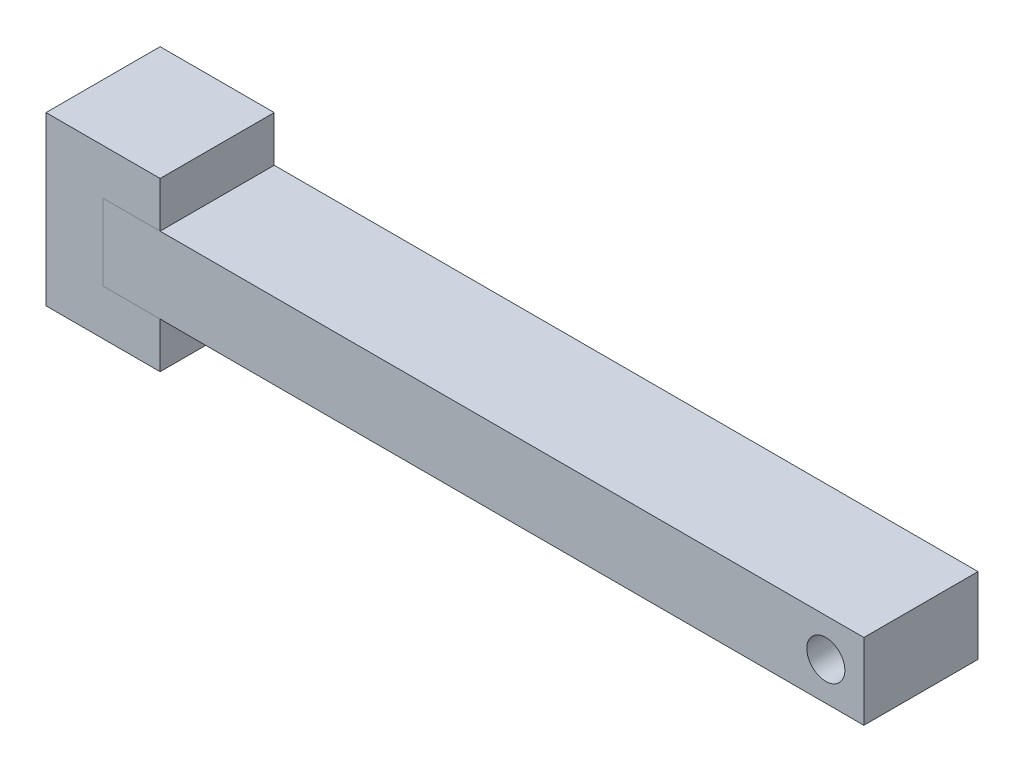
SolidWorks part; units mm, degrees
other "COLL.BOX-Boss-Extrude3"
ref_plane "Piano frontale" through (0, 0, 0) normal (0, 0, 1) x (1, 0, 0)
ref_plane "Piano superiore" through (0, 0, 0) normal (0, 1, 0) x (1, 0, 0)
ref_plane "Piano destro" through (0, 0, 0) normal (1, 0, 0) x (0, 0, -1)
sketch "Sketch1" plane through (0, 0, 0) normal (0, 1, 0) x (1, 0, 0)
  line L1 (-500, -75) -> (500, -75)
  line L2 (-500, -75) -> (-500, 75)
  line L3 (-500, 75) -> (500, 75)
  line L4 (500, -75) -> (500, 75)
  line L5 (-500, -75) -> (500, 75) construction
  line L6 (-500, 75) -> (500, -75) construction
  point P0 (0, 0)
  dimension "D1" = 150
  dimension "D2" = 1000
extrude "Boss-Extrude1" add sketch "Sketch1" along normal mid plane 100
sketch "Sketch2" plane through (0, 0, 75) normal (0, 0, 1) x (1, 0, 0)
  line L0 (500, 50) -> (500, -50) construction
  circle A0 centre (450, 0) radius 25
  dimension "D1" = 50
  dimension "D2" = 50
extrude "Cut-Extrude1" cut sketch "Sketch2" against normal through all
sketch "Sketch4" plane through (0, 0, -75) normal (0, 0, -1) x (-1, 0, 0)
  line L0 (500, 50) -> (500, -50) construction
  line L1 (425, -110) -> (575, -110)
  line L2 (425, -110) -> (425, 110)
  line L3 (425, 110) -> (575, 110)
  line L4 (575, -110) -> (575, 110)
  line L5 (425, -110) -> (575, 110) construction
  line L6 (425, 110) -> (575, -110) construction
  point P0 (500, 0)
  dimension "D1" = 220
  dimension "D2" = 150
extrude "Boss-Extrude3" add sketch "Sketch4" against normal up to surface (150 mm away) separate body up to face at (475, 0, 75)
